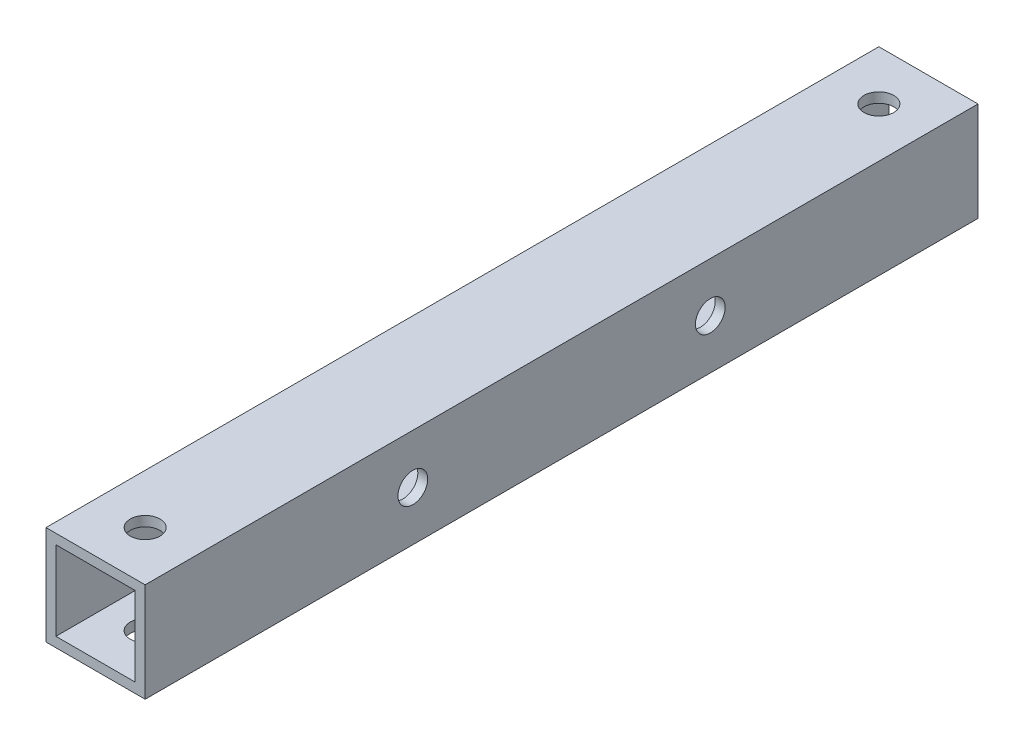
SolidWorks part; units mm, degrees
material "6063-O"
ref_plane "前视基准面" through (0, 0, 0) normal (0, 0, 1) x (1, 0, 0)
ref_plane "上视基准面" through (0, 0, 0) normal (0, 1, 0) x (1, 0, 0)
ref_plane "右视基准面" through (0, 0, 0) normal (1, 0, 0) x (0, 0, -1)
other "Configuration Table"
sketch "草图1" plane through (0, 0, 0) normal (0, 0, 1) x (1, 0, 0)
  line L1 (-5, 5) -> (5, 5)
  line L2 (-5, 5) -> (-5, -5)
  line L3 (-5, -5) -> (5, -5)
  line L4 (5, 5) -> (5, -5)
  line L5 (-5, 5) -> (5, -5) construction
  line L6 (-5, -5) -> (5, 5) construction
  point P4 (0, 0)
  dimension "D1" = 10
  dimension "D2" = 10
extrude "拉伸-薄壁1" add sketch "草图1" along normal blind 84 thin
sketch "草图2" plane through (5, 0, 0) normal (1, 0, 0) x (0, 0, -1)
  line L0 (0, 0) -> (-84, 0) construction
  line L1 (0, -5) -> (0, 5) construction
  line L2 (-84, -5) -> (-84, 5) construction
  line L3 (-42, 0) -> (-42, -5) construction
  line L4 (-84, -5) -> (0, -5) construction
  circle A0 centre (-57, 0) radius 1.5
  circle A1 centre (-27, 0) radius 1.5
  circle A2 centre (-42, 0) radius 1.5 construction
  dimension "D1" = 3
  dimension "D2" = 15
  dimension "D3" = 3
extrude "切除-拉伸1" cut sketch "草图2" against normal through all
sketch "草图3" plane through (0, 5, 0) normal (0, 1, 0) x (1, 0, 0)
  line L0 (0, 0) -> (0, -84) construction
  line L1 (5, 0) -> (-5, 0) construction
  line L2 (5, -84) -> (-5, -84) construction
  line L3 (0, -42) -> (-5, -42) construction
  line L4 (-5, -84) -> (-5, 0) construction
  circle A0 centre (0, -5) radius 1.5
  circle A3 centre (0, -79) radius 1.5
  dimension "D1" = 3
  dimension "D3" = 5
extrude "切除-拉伸2" cut sketch "草图3" against normal blind 10
